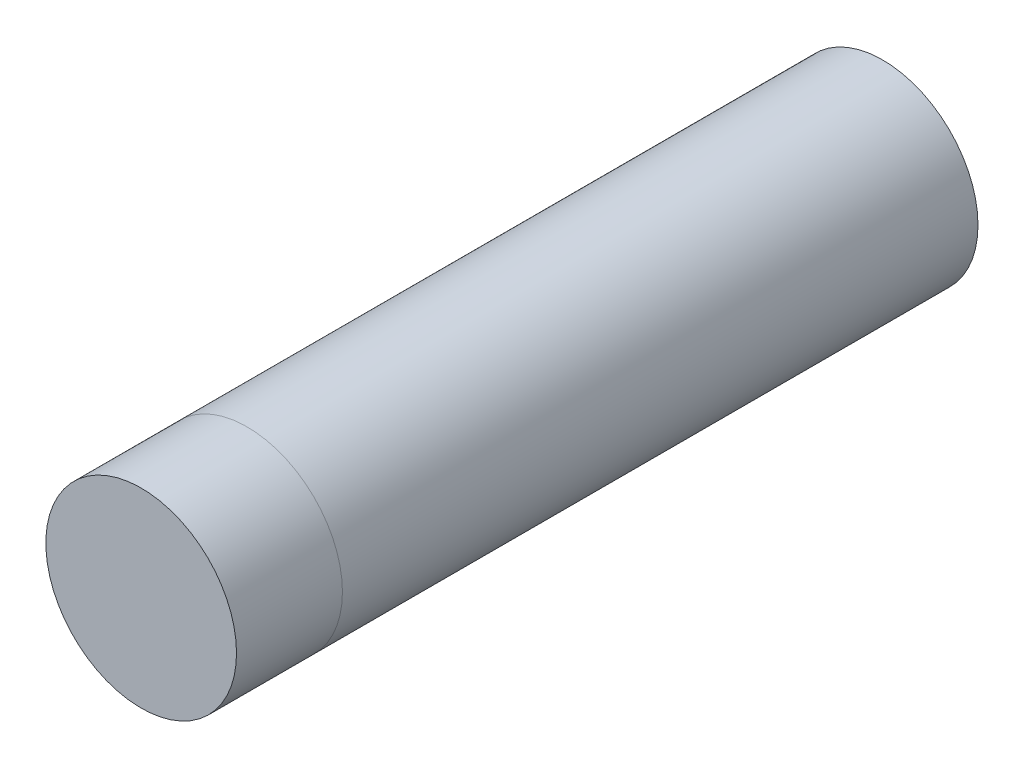
SolidWorks part; units mm, degrees
ref_plane "Front Plane" through (0, 0, 0) normal (0, 0, 1) x (1, 0, 0)
ref_plane "Top Plane" through (0, 0, 0) normal (0, 1, 0) x (1, 0, 0)
ref_plane "Right Plane" through (0, 0, 0) normal (1, 0, 0) x (0, 0, -1)
sketch "Sketch1" plane through (0, 0, 0) normal (0, 0, 1) x (1, 0, 0)
  circle A0 centre (0, 0) radius 9
  dimension "D1" = 18
extrude "Boss-Extrude1" add sketch "Sketch1" along normal blind 60
sketch "Sketch2" plane through (0, 0, 60) normal (0, 0, 1) x (1, 0, 0)
  circle A0 centre (0, 0) radius 9
extrude "Boss-Extrude2" add sketch "Sketch2" along normal blind 10 separate body
